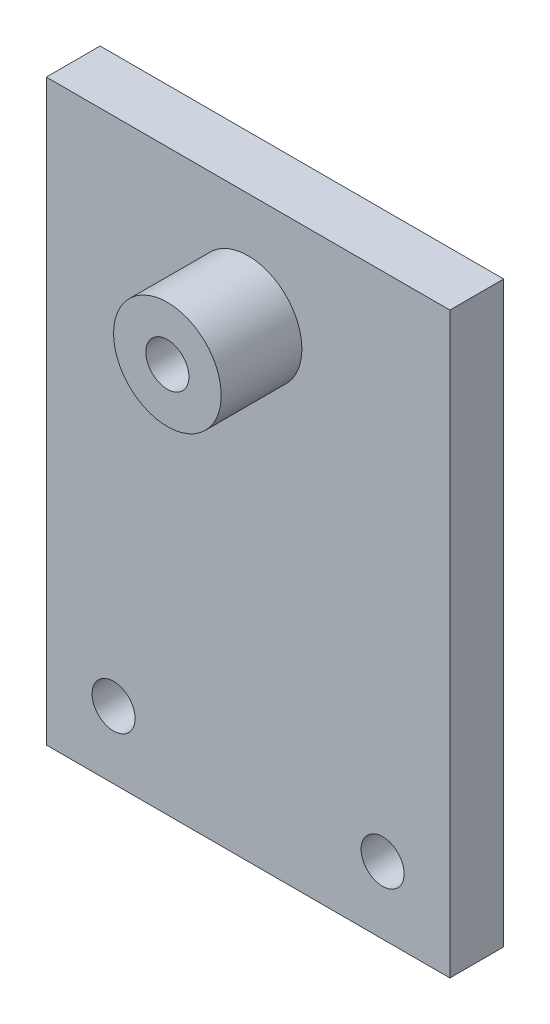
SolidWorks part; units mm, degrees
ref_plane "前视基准面" through (0, 0, 0) normal (0, 0, 1) x (1, 0, 0)
ref_plane "上视基准面" through (0, 0, 0) normal (0, 1, 0) x (1, 0, 0)
ref_plane "右视基准面" through (0, 0, 0) normal (1, 0, 0) x (0, 0, -1)
other "Configuration Table"
sketch "草图1" plane through (0, 0, 0) normal (0, 0, 1) x (1, 0, 0)
  line L0 (-30, 8.1585) -> (0, 8.1585) construction
  line L1 (-30, 46.1585) -> (0, 46.1585)
  line L2 (-30, 46.1585) -> (-30, 3.1585)
  line L3 (-30, 3.1585) -> (0, 3.1585)
  line L4 (0, 46.1585) -> (0, 3.1585)
  line L5 (-15, 46.1585) -> (-15, 3.1585) construction
  circle A0 centre (-5, 8.1585) radius 1.6
  circle A1 centre (-25, 8.1585) radius 1.6
  circle A2 centre (-15, 38.1585) radius 4
  point P12 (-15, 8.1585)
  dimension "D2" = 10
  dimension "D4" = 3.2
  dimension "D6" = 8
  dimension "D1" = 30
  dimension "D3" = 10
  dimension "D5" = 5
  dimension "D7" = 30
  dimension "D8" = 8
extrude "凸台-拉伸1" add sketch "草图1" along normal blind 4 contours A2 | L2 L1 L4 L3 | A1 | A0
sketch "草图2" plane through (0, 0, 4) normal (0, 0, 1) x (1, 0, 0)
  circle A0 centre (-15, 38.1585) radius 4
  circle A1 centre (-15, 38.1585) radius 4 construction
extrude "凸台-拉伸2" add sketch "草图2" along normal blind 10 from surface at -4 starting at face at (-23.4, 8.1585, 0)
sketch "草图3" plane through (0, 0, 10) normal (0, 0, 1) x (1, 0, 0)
  circle A0 centre (-15, 38.1585) radius 1.6
  dimension "D1" = 3.2
extrude "切除-拉伸1" cut sketch "草图3" against normal through all
sketch "草图4" plane through (0, 0, 0) normal (0, 0, -1) x (-1, 0, 0)
  circle A0 centre (15, 38.1585) radius 3.5
  dimension "D1" = 7
